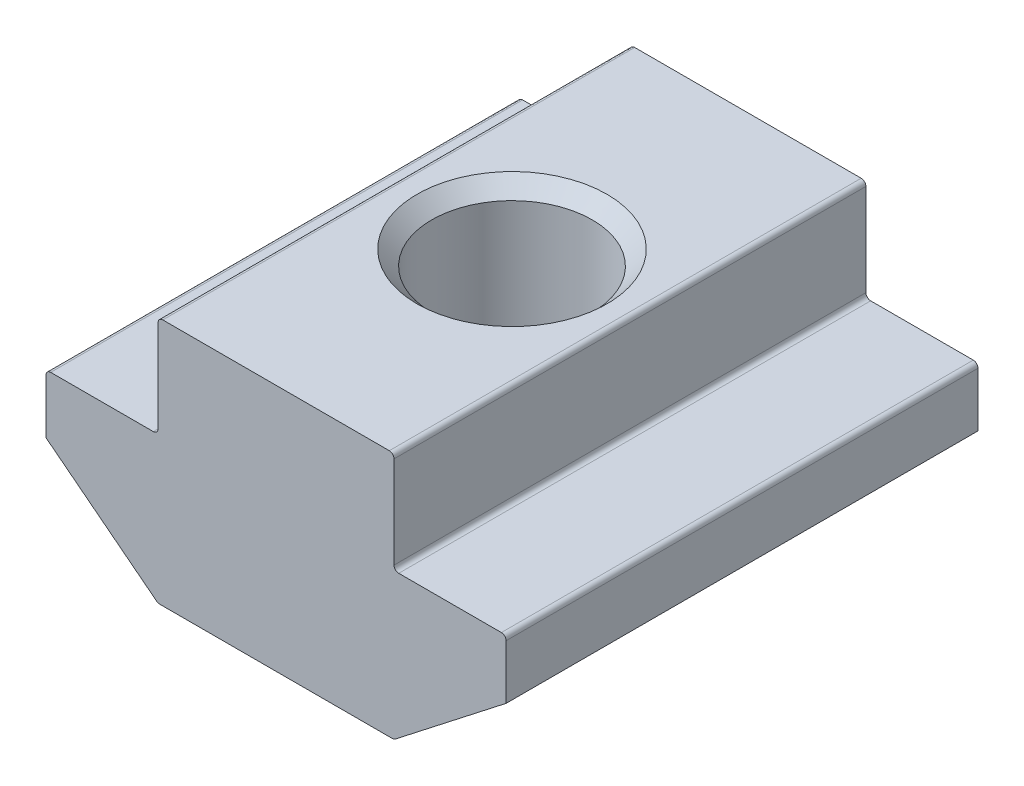
SolidWorks part; units mm, degrees
ref_plane "Спереди" through (0, 0, 0) normal (0, 0, 1) x (1, 0, 0)
ref_plane "Сверху" through (0, 0, 0) normal (0, 1, 0) x (1, 0, 0)
ref_plane "Справа" through (0, 0, 0) normal (1, 0, 0) x (0, 0, -1)
sketch "Эскиз1" plane through (0, 0, 0) normal (0, 0, 1) x (1, 0, 0)
  line L0 (5, 0) -> (-5, 0)
  line L1 (-5, 0) -> (-5, -4.3)
  line L2 (-5, -4.3) -> (-9.75, -4.3)
  line L3 (-9.75, -4.3) -> (-9.75, -6.8)
  line L4 (-9.75, -6.8) -> (-5, -10.5)
  line L5 (-5, -10.5) -> (5, -10.5)
  line L6 (0, -10.5) -> (0, 0) construction
  line L7 (9.75, -6.8) -> (5, -10.5)
  line L8 (9.75, -4.3) -> (9.75, -6.8)
  line L9 (5, -4.3) -> (9.75, -4.3)
  line L10 (5, 0) -> (5, -4.3)
  point P3 (-5, -2.15)
  dimension "D1" = 10
  dimension "D2" = 19.5
  dimension "D3" = 2.5
  dimension "D4" = 10.5
  dimension "D5" = 6.2
extrude "Бобышка-Вытянуть1" add sketch "Эскиз1" along normal mid plane 20
hole_wizard "Отверстие обработанное метчиком M83" positions "Эскиз2" profile "Эскиз4" tap size "M8" standard "ISO" end condition through all
sketch "Эскиз2" plane through (0, 0, 0) normal (0, 1, 0) x (1, 0, 0)
  point P0 (0, 0)
sketch "Эскиз4" plane through (0, 0, 0) normal (1, 0, 0) x (0, 0, 1)
  line L0 (0, 0) -> (0, 10.5)
  line L1 (0, 10.5) -> (4.025, 10.5)
  line L2 (3.4, 9.875) -> (3.4, 0.625)
  line L3 (3.4, 0.625) -> (4.025, 0)
  line L5 (4.025, 0) -> (0, 0)
  line L6 (-3.4, 0.625) -> (-4.025, 0) construction
  line L7 (4.025, 10.5) -> (3.4, 9.875)
  line L8 (-4.025, 10.5) -> (-3.4, 9.875) construction
  line L11 (0, -6.35) -> (0, 107.95) construction
  dimension "Диаметр проходного сверла" = 6.8
  dimension "Глубина проходного сверла" = 10.5
  dimension "Диаметр передней зенковки" = 8.05
  dimension "Угол передней зенковки" = 90
  dimension "Диаметр задней зенковки" = 8.05
  dimension "Угол задней зенковки" = 90
cosmetic thread "Отверстие резьбы1" parameters "D2"=8
fillet "Скругление1" radius 0.2 8 edges at (5, -10.5, 0) (-5, -10.5, 0) (9.75, -4.3, 0) (5, -4.3, 0) (5, 0, 0) (-5, 0, 0) (-9.75, -4.3, 0) (-5, -4.3, 0)
